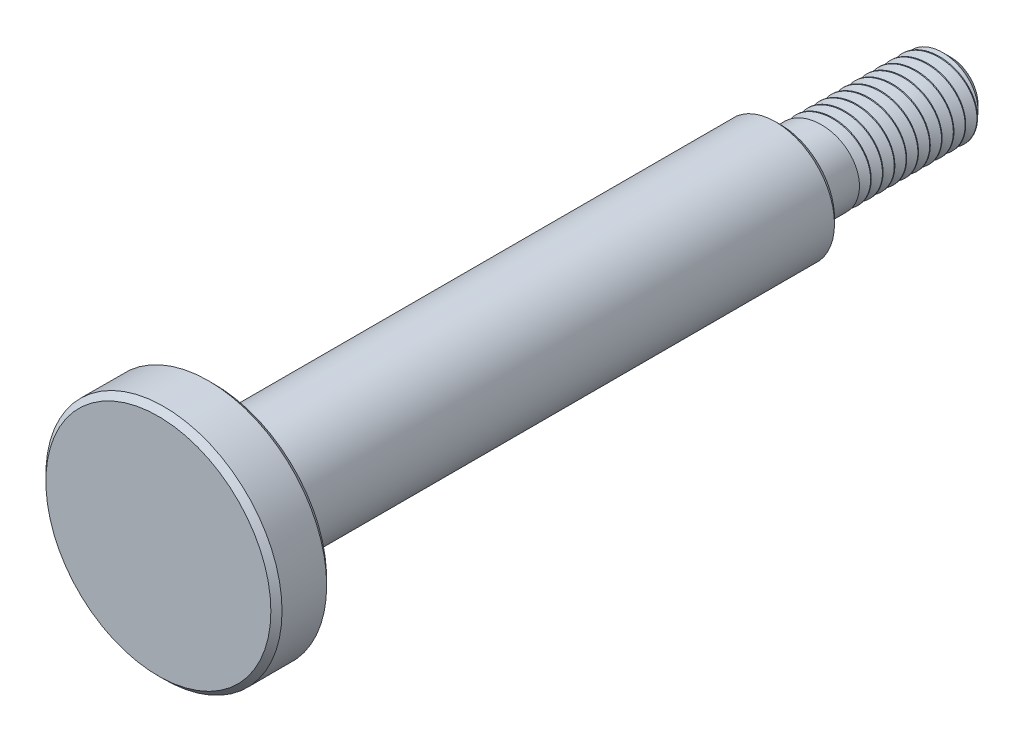
SolidWorks part; units mm, degrees
ref_plane "Front" through (0, 0, 0) normal (0, 0, 1) x (1, 0, 0)
ref_plane "Top" through (0, 0, 0) normal (0, 1, 0) x (1, 0, 0)
ref_plane "Right" through (0, 0, 0) normal (1, 0, 0) x (0, 0, -1)
sketch "Sketch1" plane through (0, 0, 0) normal (0, 1, 0) x (1, 0, 0)
  line L0 (0, 0) -> (0, 26.6665) construction
  line L1 (0, 9.144) -> (2.0828, 9.144)
  line L2 (2.0828, 9.144) -> (2.0828, 0)
  line L3 (2.0828, 0) -> (3.175, 0)
  line L4 (3.175, 0) -> (3.175, -30.4786)
  line L5 (3.175, -30.4786) -> (6.35, -30.4786)
  line L6 (6.35, -30.4786) -> (6.35, -33.4786)
  line L7 (6.35, -33.4786) -> (0, -33.4786)
  line L8 (0, -33.4786) -> (0, 9.144)
  dimension "D1" = 6.35
  dimension "D2" = 4.1656
  dimension "D3" = 12.7
  dimension "D4" = 3
  dimension "D5" = 30.4786
  dimension "D6" = 9.144
revolve "Revolve1" add sketch "Sketch1" angle 360 about L0
sketch "Sketch2" [suppressed] plane through (0, 0, 0) normal (0, 1, 0) x (1, 0, 0)
  line L0 (0, 0) -> (0, -12.324) construction
  line L1 (6.35, -29) -> (3.175, -25.825)
  line L3 (3.175, -25.825) -> (3.175, -29)
  line L4 (3.175, -29) -> (6.35, -29)
revolve "Revolve2" [suppressed] add sketch "Sketch2" angle 360 about L0
chamfer "Chamfer1" distance 0.3 angle 45 2 edges at (6.35, 0, 33.4786) (3.175, 0, 0)
chamfer "Chamfer2" distance 0.3 angle 45 1 edges at (6.35, 0, 30.4786)
chamfer "Chamfer3" distance 0.635 angle 45 1 edges at (2.0828, 0, -9.144)
sketch "Sketch3" plane through (0, 0, 0) normal (0, 1, 0) x (1, 0, 0)
  line L0 (0, 9.144) -> (0, 11.1791) construction
  line L1 (1.4478, 9.144) -> (-1.4478, 9.144) construction
  line L2 (-4.5318, 8.5892) -> (4.6332, 9.7112) construction
  line L3 (-2.1605, 9.2018) -> (-2.0828, 8.5668)
  line L4 (-2.0828, 8.509) -> (-2.0828, 0) construction
  line L5 (-2.0828, 8.5668) -> (-1.5717, 8.9516)
  line L6 (-1.5717, 8.9516) -> (-2.1605, 9.2018)
  line L7 (-2.0828, 8.5668) -> (0, 8.5668) construction
  line L8 (-1.5717, 8.9516) -> (1.5717, 8.9516) construction
  line L9 (-1.5717, 8.9516) -> (-1.5717, 8.5668) construction
  line L10 (1.5717, 8.9516) -> (1.5717, 9.3364) construction
  line L11 (0, 9.144) -> (-0.2467, 11.1593) construction
  point P11 (0, 8.9516)
  dimension "D1" = 0.635
revolve "8-32 sim" cut sketch "Sketch3" angle 360 about L11
pattern_linear "LPattern1" count 8 spacing 0.635 along (0, 0, 1) count 2 spacing 2.54 along (0, 0, 1) of "8-32 sim"
